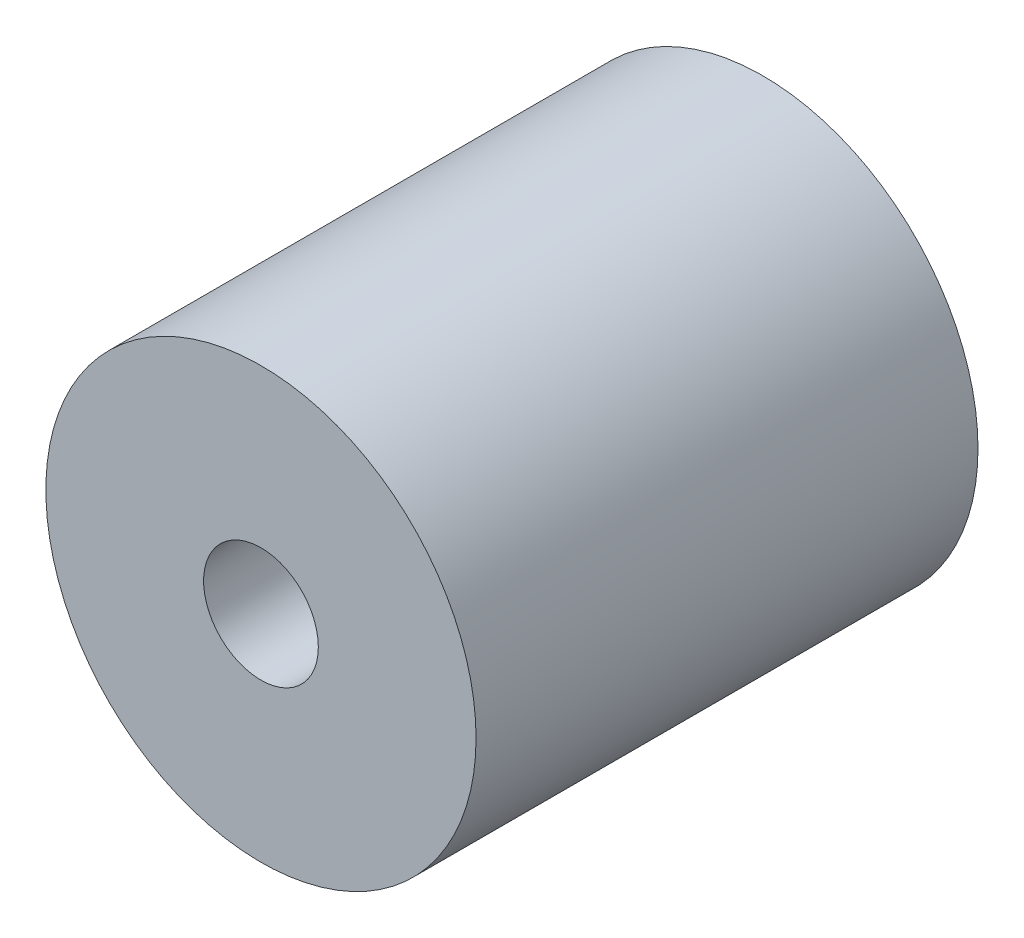
SolidWorks part; units mm, degrees
material "7079 Alloy"
ref_plane "Front" through (0, 0, 0) normal (0, 0, 1) x (1, 0, 0)
ref_plane "Top" through (0, 0, 0) normal (0, 1, 0) x (1, 0, 0)
ref_plane "Right" through (0, 0, 0) normal (1, 0, 0) x (0, 0, -1)
sketch "Sketch1" plane through (0, 0, 0) normal (0, 0, 1) x (1, 0, 0)
  circle A0 centre (0, 0) radius 15
extrude "Extrude1" add sketch "Sketch1" along normal blind 35
sketch "Sketch2" plane through (0, 0, 35) normal (0, 0, 1) x (1, 0, 0)
  circle A0 centre (0, 0) radius 4
extrude "Cut-Extrude1" cut sketch "Sketch2" against normal blind 10
sketch "Sketch3" plane through (0, 0, 0) normal (0, 0, -1) x (-1, 0, 0)
  circle A0 centre (0, 0) radius 6
extrude "Cut-Extrude2" cut sketch "Sketch3" against normal blind 10
